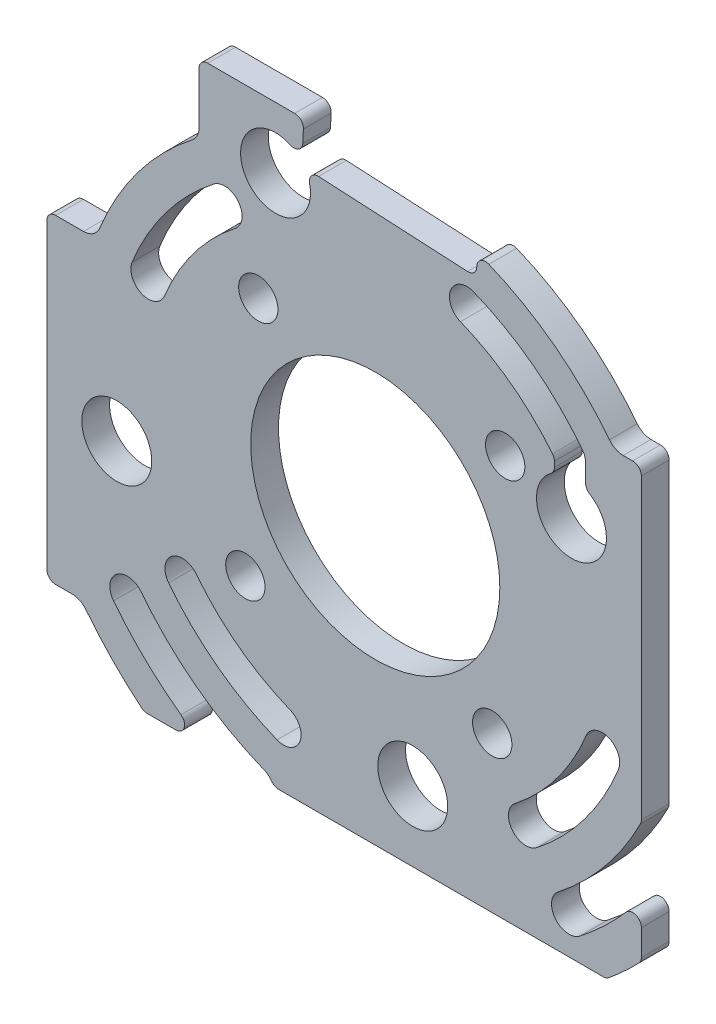
SolidWorks part; units mm, degrees
material "MDF"
ref_plane "Front Plane" through (0, 0, 0) normal (0, 0, 1) x (1, 0, 0)
ref_plane "Top Plane" through (0, 0, 0) normal (0, 1, 0) x (1, 0, 0)
ref_plane "Right Plane" through (0, 0, 0) normal (1, 0, 0) x (0, 0, -1)
sketch "Sketch1" plane through (0, 0, 0) normal (0, 0, 1) x (1, 0, 0)
  line L0 (-6.6325, 45.4094) -> (11.3428, 44.4673) construction
  line L1 (30.4449, -32.63) -> (-37.573, -32.63)
  line L2 (30.4449, -32.63) -> (30.4449, 48.4731)
  line L3 (30.4449, 48.4731) -> (-37.573, 52.0377)
  line L4 (-37.573, -32.63) -> (-37.573, 52.0377)
  circle A0 centre (0, 0) radius 20 construction
  circle A1 centre (0, 0) radius 14.25
  circle A5 centre (-29.573, -7.3783) radius 4
  circle A6 centre (-11.4133, 28.2619) radius 4
  circle A7 centre (22.4449, 11.0103) radius 4
  circle A8 centre (4.2853, -24.63) radius 4
  point P0 (0, 0)
  dimension "D1" = 40
  dimension "D3" = 28.5
  dimension "D4" = 8
  dimension "D6" = 8
  dimension "D7" = 8
  dimension "D5" = 8
  dimension "D2" = 5
extrude "Boss-Extrude1" add sketch "Sketch1" along normal blind 3.175
hole_wizard "M4 Clearance Hole1" positions "Sketch2" profile "Sketch3" hole size "M4" standard "ANSI Metric" end condition through all
sketch "Sketch2" plane through (0, 0, 0) normal (0, 0, -1) x (-1, 0, 0)
  line L0 (14.8629, -13.3826) -> (-14.8629, 13.3826) construction
  line L1 (13.3826, 14.8629) -> (-13.3826, -14.8629) construction
  circle A0 centre (0, 0) radius 20 construction
  point P18 (-14.8629, 13.3826)
  point P24 (13.3826, 14.8629)
  point P27 (14.8629, -13.3826)
  point P30 (-13.3826, -14.8629)
sketch "Sketch3" plane through (14.8629, 13.3826, 0) normal (1, 0, 0) x (0, 1, 0)
  line L0 (0, 0) -> (0, 3.175)
  line L1 (0, 3.175) -> (2.25, 3.175)
  line L2 (2.25, 3.175) -> (2.25, 0)
  line L5 (2.25, 0) -> (0, 0)
  line L11 (0, -6.35) -> (0, 107.95) construction
  dimension "Thru Hole Dia." = 4.5
  dimension "Thru Hole Depth" = 3.175
sketch "Sketch4" plane through (0, 0, 0) normal (0, 0, 1) x (1, 0, 0)
  arc A4 (-23.3951, 29.9444) -> (-35.233, 14.2351) centre (0, 0) ccw
  arc A5 (-35.233, 14.2351) -> (-31.5243, 12.7366) centre (-33.3786, 13.4858) ccw
  arc A6 (-20.9325, 26.7924) -> (-31.5243, 12.7366) centre (0, 0) ccw
  arc A7 (-20.9325, 26.7924) -> (-23.3951, 29.9444) centre (-22.1638, 28.3684) ccw
  arc A8 (-23.3951, 29.9444) -> (-35.233, 14.2351) centre (0, 0) ccw
  arc A9 (-35.233, 14.2351) -> (-31.5243, 12.7366) centre (-33.3786, 13.4858) ccw
  arc A10 (-20.9325, 26.7924) -> (-31.5243, 12.7366) centre (0, 0) ccw
  arc A11 (-20.9325, 26.7924) -> (-23.3951, 29.9444) centre (-22.1638, 28.3684) ccw
  arc A12 (-18.4698, 23.6403) -> (-27.8155, 11.2382) centre (0, 0) ccw
  arc A13 (-27.8155, 11.2382) -> (-24.1068, 9.7398) centre (-25.9611, 10.489) ccw
  arc A14 (-16.0072, 20.4883) -> (-24.1068, 9.7398) centre (0, 0) ccw
  arc A15 (-16.0072, 20.4883) -> (-18.4698, 23.6403) centre (-17.2385, 22.0643) ccw
  arc A16 (-18.4698, 23.6403) -> (-27.8155, 11.2382) centre (0, 0) ccw
  arc A17 (-27.8155, 11.2382) -> (-24.1068, 9.7398) centre (-25.9611, 10.489) ccw
  arc A18 (-16.0072, 20.4883) -> (-24.1068, 9.7398) centre (0, 0) ccw
  arc A19 (-16.0072, 20.4883) -> (-18.4698, 23.6403) centre (-17.2385, 22.0643) ccw
  arc A20 (-42.6505, 17.2319) -> (-38.9417, 15.7335) centre (-40.7961, 16.4827) ccw
  arc A21 (-25.8578, 33.0965) -> (-38.9417, 15.7335) centre (0, 0) ccw
  arc A22 (-25.8578, 33.0965) -> (-28.3204, 36.2485) centre (-27.0891, 34.6725) ccw
  arc A23 (-28.3204, 36.2485) -> (-42.6505, 17.2319) centre (0, 0) ccw
  arc A24 (-42.6505, 17.2319) -> (-38.9417, 15.7335) centre (-40.7961, 16.4827) ccw
  arc A25 (-25.8578, 33.0965) -> (-38.9417, 15.7335) centre (0, 0) ccw
  arc A26 (-25.8578, 33.0965) -> (-28.3204, 36.2485) centre (-27.0891, 34.6725) ccw
  arc A27 (-28.3204, 36.2485) -> (-42.6505, 17.2319) centre (0, 0) ccw
  dimension "D1" = 0
  dimension "D2" = 0
  dimension "D3" = 0
extrude "VentHoles" cut sketch "Sketch4" along normal through all
pattern_circular "CirPattern1" count 4 over 360 about axis through (0, 0, 0) along (0, 0, 1) of "VentHoles"
sketch "Sketch5" plane through (0, 0, 0) normal (0, 0, 1) x (1, 0, 0)
  line L1 (12.3414, 44.415) -> (11.5564, 29.4355)
  line L2 (12.2891, 43.4163) -> (11.9202, 36.3769) construction
  line L3 (-7.6835, 44.4631) -> (-8.3639, 31.4809) construction
  line L4 (-6.6325, 45.4094) -> (11.3428, 44.4673) construction
  line L5 (-8.4162, 30.4822) -> (11.5564, 29.4355)
  line L6 (-7.6312, 45.4617) -> (-8.4162, 30.4822)
  line L7 (-7.6312, 45.4617) -> (12.3414, 44.415)
  line L8 (-7.4176, 30.4299) -> (10.5577, 29.4879) construction
  line L10 (-7.4176, 30.4299) -> (10.5577, 29.4879) construction
extrude "Cut-Extrude2" cut sketch "Sketch5" along normal through all
sketch "Sketch7" plane through (0, 0, 0) normal (0, 0, 1) x (1, 0, 0)
  line L0 (-37.573, 52.0377) -> (-37.573, 26.5381) construction
  line L1 (-37.573, 35.2619) -> (30.4449, 35.2619)
  line L2 (-37.573, 35.2619) -> (-37.573, 48.4731)
  line L3 (-37.573, 48.4731) -> (30.4449, 48.4731)
  line L4 (30.4449, 35.2619) -> (30.4449, 48.4731)
  arc A0 (-8.395, 30.8867) -> (-8.0743, 30.4643) centre (-11.4133, 28.2619) ccw construction
  dimension "D1" = 7
extrude "Cut-Extrude3" cut sketch "Sketch7" against normal through all both and the other way through all
delete or keep bodies "Body-Delete/Keep 1" type delete bodies bodies 114 116 118 115
sketch "Sketch9" plane through (0, 0, 3.175) normal (0, 0, 1) x (1, 0, 0)
  line L0 (20.4883, 16.0072) -> (20.4883, 14.4991)
  line L1 (24.0643, 17.2385) -> (24.0643, 14.6678)
  circle A0 centre (22.4449, 11.0103) radius 4 construction
  arc A2 (20.4883, 16.0072) -> (23.6403, 18.4698) centre (22.0643, 17.2385) ccw construction
  circle A3 centre (22.4449, 11.0103) radius 4
  arc A4 (20.4883, 16.0072) -> (23.6403, 18.4698) centre (22.0643, 17.2385) ccw
extrude "Cut-Extrude4" cut sketch "Sketch9" against normal through all both and the other way through all contours A4 L0 A3 L1
sketch "Sketch10" plane through (0, 0, 3.175) normal (0, 0, 1) x (1, 0, 0)
  line L0 (-34.6725, -25.0891) -> (-37.573, -25.0891)
  line L1 (-37.573, 18.7689) -> (-37.573, -32.63) construction
  line L2 (28.3684, 20.1638) -> (30.4449, 20.1638)
  line L3 (30.4449, -15.1363) -> (30.4449, 28.9328) construction
  line L4 (-37.573, -25.0891) -> (-37.573, -32.63)
  line L5 (-37.573, -32.63) -> (-30.4501, -32.63)
  line L6 (-30.4501, -32.63) -> (-34.6725, -25.0891)
  line L7 (30.4449, 20.1638) -> (30.4449, 36.986)
  line L8 (30.4449, 36.986) -> (11.7757, 36.986)
  line L9 (11.7757, 36.986) -> (28.3684, 20.1638)
  line L10 (-20.1638, 28.3684) -> (-20.1638, 35.2619)
  line L11 (-25.1779, 35.2619) -> (-8.1657, 35.2619) construction
  line L12 (-33.3786, 11.4858) -> (-37.573, 11.4858)
  line L13 (-25.1779, 35.2619) -> (-8.1657, 35.2619)
  line L14 (-37.573, 18.7689) -> (-37.573, -32.63)
  arc A0 (-33.0965, -25.8578) -> (-36.2485, -28.3204) centre (-34.6725, -27.0891) ccw construction
  arc A1 (26.7924, 20.9325) -> (29.9444, 23.3951) centre (28.3684, 22.1638) ccw construction
  arc A2 (-20.9325, 26.7924) -> (-23.3951, 29.9444) centre (-22.1638, 28.3684) ccw construction
  arc A3 (-35.233, 14.2351) -> (-31.5243, 12.7366) centre (-33.3786, 13.4858) ccw construction
  arc A4 (-25.8578, 33.0965) -> (-25.1779, 35.2619) centre (-27.0891, 34.6725) ccw construction
  arc A5 (-25.8578, 33.0965) -> (-37.573, 18.7689) centre (0, 0) ccw construction
  arc A6 (-25.8578, 33.0965) -> (-25.1779, 35.2619) centre (-27.0891, 34.6725) ccw
  arc A7 (-25.8578, 33.0965) -> (-37.573, 18.7689) centre (0, 0) ccw
  arc A8 (-23.3951, 29.9444) -> (-35.233, 14.2351) centre (0, 0) ccw construction
  arc A9 (-20.9325, 26.7924) -> (-23.3951, 29.9444) centre (-22.1638, 28.3684) ccw
  arc A10 (-35.233, 14.2351) -> (-31.5243, 12.7366) centre (-33.3786, 13.4858) ccw
  arc A11 (-23.3951, 29.9444) -> (-35.233, 14.2351) centre (0, 0) ccw
extrude "Cut-Extrude5" cut sketch "Sketch10" against normal through all both and the other way through all contours L5 L6 L0 L4 | L8 L9 L2 L7 | A11 A9 L10 L13 A6 A7 L14 L12 A10
fillet "Fillet1" radius 1 19 edges at (30.4449, -28.9328, 1.5875) (26.444, -32.63, 1.5875) (-11.6312, -32.63, 1.5875) (-19.4752, -32.63, 1.5875) (11.7144, 32.4502, 1.5875) (-8.1657, 35.2619, 1.5875) (-26.444, -32.63, 1.5875) (11.5564, 29.4355, 1.5875) (-8.395, 30.8867, 1.5875) (-8.0743, 30.4643, 1.5875) (20.4883, 16.0072, 1.5875) (20.4883, 14.4991, 1.5875) (24.0643, 14.6678, 1.5875) (30.4449, -22.74, 1.5875) (-37.573, -25.0891, 1.5875) (30.4449, -15.1363, 1.5875) (30.4449, 20.1638, 1.5875) (-20.1638, 35.2619, 1.5875) (-37.573, 11.4858, 1.5875)
